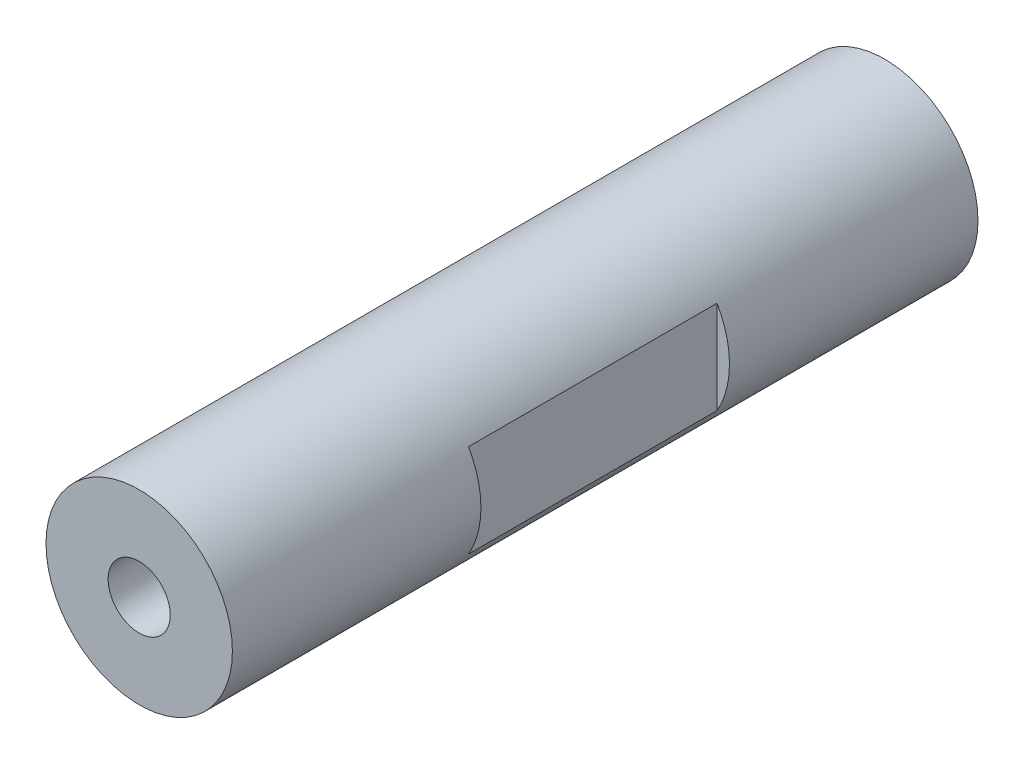
SolidWorks part; units mm, degrees
ref_plane "前视基准面" through (0, 0, 0) normal (0, 0, 1) x (1, 0, 0)
ref_plane "上视基准面" through (0, 0, 0) normal (0, 1, 0) x (1, 0, 0)
ref_plane "右视基准面" through (0, 0, 0) normal (1, 0, 0) x (0, 0, -1)
sketch "草图1" plane through (0, 0, 0) normal (0, 0, 1) x (1, 0, 0)
  circle A0 centre (0, 0) radius 7.5
  dimension "D1" = 15
extrude "凸台-拉伸1" add sketch "草图1" along normal mid plane 60
sketch "草图2" plane through (0, 0, 0) normal (0, 1, 0) x (1, 0, 0)
  line L0 (-7.5, 30) -> (-7.5, -30) construction
  line L1 (-6.5, -10) -> (-8.5, -10)
  line L2 (-6.5, -10) -> (-6.5, 10)
  line L3 (-6.5, 10) -> (-8.5, 10)
  line L4 (-8.5, -10) -> (-8.5, 10)
  line L5 (-6.5, -10) -> (-8.5, 10) construction
  line L6 (-6.5, 10) -> (-8.5, -10) construction
  line L7 (0, 0) -> (0, -10.8537) construction
  line L8 (6.5, 10) -> (8.5, -10) construction
  line L9 (6.5, -10) -> (8.5, 10) construction
  line L10 (8.5, -10) -> (8.5, 10)
  line L11 (6.5, 10) -> (8.5, 10)
  line L12 (6.5, -10) -> (6.5, 10)
  line L13 (6.5, -10) -> (8.5, -10)
  point P0 (-7.5, 0)
  point P14 (7.5, 0)
  dimension "D1" = 13
  dimension "D2" = 20
extrude "切除-拉伸1" cut sketch "草图2" against normal mid plane 20
sketch "草图3" plane through (0, 0, -30) normal (0, 0, -1) x (-1, 0, 0)
  circle A0 centre (0, 0) radius 3.5913
hole_wizard "M6 螺纹孔1" positions "3D草图1" profile "草图5" tap size "M6" standard "Ks"
sketch3d "3D草图1"
  point P0 (0, 0, -30)
sketch "草图5" plane through (0, 0, -30) normal (1, 0, 0) x (0, 1, 0)
  line L0 (0, 0) -> (0, 16.5022)
  line L1 (0, 16.5022) -> (2.5, 15)
  line L2 (2.5, 15) -> (2.5, 0)
  line L5 (2.5, 0) -> (0, 0)
  line L10 (0, 16.5022) -> (-2.5, 15) construction
  line L11 (0, -6.35) -> (0, 107.95) construction
  dimension "螺纹孔钻头直径" = 5
  dimension "螺纹孔钻头深度" = 15
  dimension "导头角度" = 118
mirror "镜向1" about plane through (0, 0, 0) normal (0, 0, 1) of "M6 螺纹孔1"
